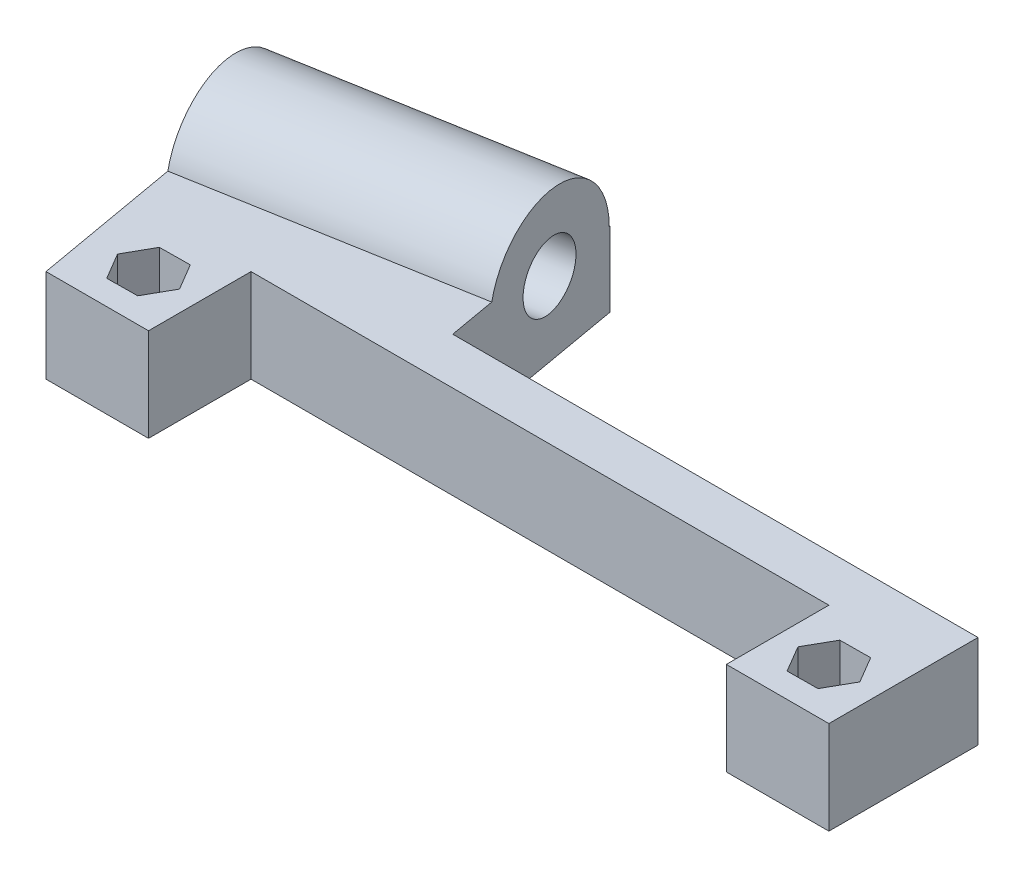
SolidWorks part; units mm, degrees
ref_plane "前视基准面" through (0, 0, 0) normal (0, 0, 1) x (1, 0, 0)
ref_plane "上视基准面" through (0, 0, 0) normal (0, 1, 0) x (1, 0, 0)
ref_plane "右视基准面" through (0, 0, 0) normal (1, 0, 0) x (0, 0, -1)
other "Configuration Table"
sketch "草图1" plane through (0, 0, 0) normal (0, 1, 0) x (1, 0, 0)
  line L0 (-42, 5.5) -> (-42, 10.5)
  line L1 (-31, 5.5) -> (31, 5.5)
  line L2 (-42, 5.5) -> (-42, -5.5)
  line L3 (-42, -5.5) -> (-31, -5.5)
  line L4 (42, 5.5) -> (42, -5.5)
  line L5 (-42, 5.5) -> (42, -5.5) construction
  line L6 (-42, -5.5) -> (42, 5.5) construction
  line L8 (-42, 10.5) -> (42, 10.5)
  line L9 (42, 10.5) -> (42, 5.5)
  line L12 (-31, 5.5) -> (-31, -5.5)
  line L13 (31, -5.5) -> (42, -5.5)
  line L14 (31, 5.5) -> (31, -5.5)
  point P0 (0, 0)
extrude "凸台-拉伸1" add sketch "草图1" along normal blind 10
sketch "草图2" plane through (0, 10, 0) normal (0, 1, 0) x (1, 0, 0)
  circle A0 centre (-36.5, 0) radius 1.5
  circle A1 centre (36.5, 0) radius 1.5
extrude "切除-拉伸1" cut sketch "草图2" against normal blind 10
sketch "草图3" plane through (0, 10, 0) normal (0, 1, 0) x (1, 0, 0)
  line L1 (-34.8262, -2.8334) -> (-33.2093, 0.0328)
  line L2 (-33.2093, 0.0328) -> (-34.8831, 2.8663)
  line L3 (-34.8831, 2.8663) -> (-38.1738, 2.8334)
  line L4 (-38.1738, 2.8334) -> (-39.7907, -0.0328)
  line L5 (-39.7907, -0.0328) -> (-38.1169, -2.8663)
  line L6 (-38.1169, -2.8663) -> (-34.8262, -2.8334)
  line L7 (38.1687, -2.8365) -> (39.7908, 0.0269)
  line L8 (39.7908, 0.0269) -> (38.1221, 2.8633)
  line L9 (38.1221, 2.8633) -> (34.8313, 2.8365)
  line L10 (34.8313, 2.8365) -> (33.2092, -0.0269)
  line L11 (33.2092, -0.0269) -> (34.8779, -2.8633)
  line L12 (34.8779, -2.8633) -> (38.1687, -2.8365)
  circle A2 centre (-36.5, 0) radius 2.85 construction
  circle A3 centre (36.5, 0) radius 2.85 construction
extrude "切除-拉伸2" cut sketch "草图3" against normal blind 6
sketch "草图4" plane through (0, 0, 0) normal (0, 1, 0) x (1, 0, 0)
  line L0 (-44.7784, 26.2569) -> (-47.5145, 25.7745)
  line L2 (-44.7784, 26.2569) -> (-17.9702, 30.9839)
  line L6 (-14.3584, 10.5) -> (-42, 10.5)
  line L7 (-42, -5.5) -> (-47.5145, 25.7745)
  line L8 (-42, 10.5) -> (-42, -5.5)
  line L10 (-17.9702, 30.9839) -> (-14.3584, 10.5)
extrude "凸台-拉伸2" add sketch "草图4" along normal blind 16
sketch "草图5" plane through (-12.1298, 0, 2.1388) normal (0.9848, 0, -0.1736) x (-0.1736, 0, -0.9848)
  line L4 (33.5337, 8) -> (33.6337, 8)
  line L6 (33.6337, 16) -> (33.6337, 0) construction
  line L9 (33.6337, 8) -> (33.6337, 16)
  line L10 (33.6337, 16) -> (1.8768, 16)
  line L11 (1.8768, 16) -> (1.8768, 10)
  line L12 (1.8768, 10) -> (12.8338, 10)
  line L13 (3.0473, 10) -> (12.8338, 10) construction
  line L14 (17.6337, 10) -> (1.8768, 10) construction
  line L15 (12.8338, 10) -> (17.9911, 10)
  arc A2 (33.5337, 8) -> (17.9911, 10) centre (25.6337, 8) ccw
extrude "切除-拉伸3" cut sketch "草图5" against normal through all and the other way through all
sketch "草图6" plane through (-12.1298, 0, 2.1388) normal (0.9848, 0, -0.1736) x (-0.1736, 0, -0.9848)
  circle A0 centre (25.6337, 8) radius 3.5
extrude "切除-拉伸4" cut sketch "草图6" against normal through all
sketch "草图8" plane through (-41.6741, 0, 7.3483) normal (-0.9848, 0, 0.1736) x (0.1736, 0, 0.9848)
  circle A0 centre (-25.6337, 8) radius 5.25
extrude "切除-拉伸6" cut sketch "草图8" against normal blind 24
